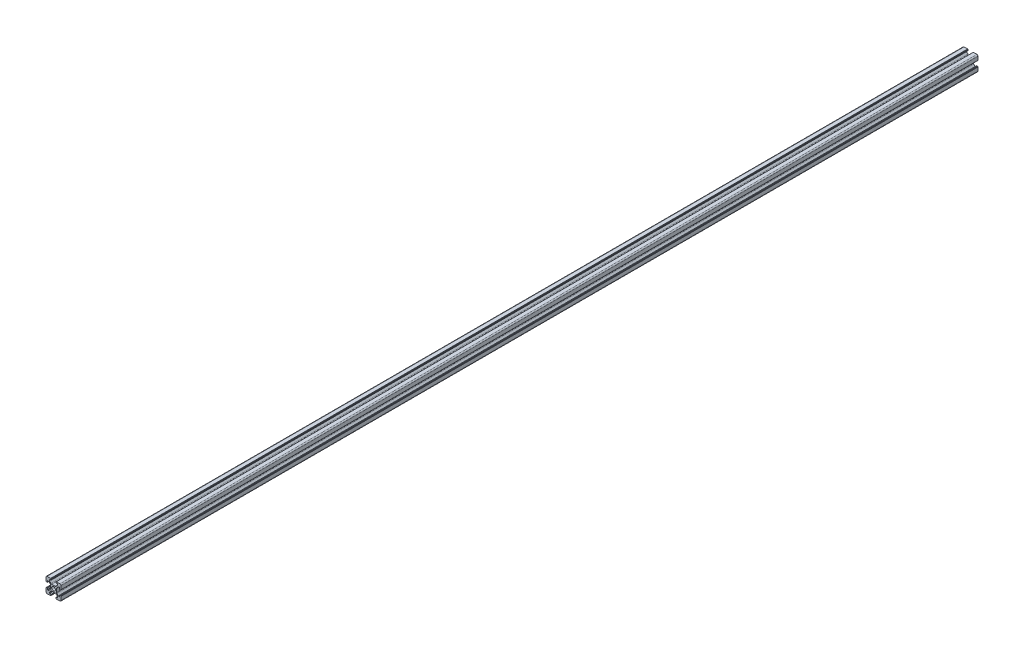
SolidWorks part; units mm, degrees
material "1060 Alloy"
ref_plane "前视基准面" through (0, 0, 0) normal (0, 0, 1) x (1, 0, 0)
ref_plane "上视基准面" through (0, 0, 0) normal (0, 1, 0) x (1, 0, 0)
ref_plane "右视基准面" through (0, 0, 0) normal (1, 0, 0) x (0, 0, -1)
sketch "草图1" plane through (0, 0, 0) normal (0, 0, 1) x (1, 0, 0)
  line L0 (0, 0) -> (0, 5.5) construction
  line L1 (-8.5023, -10.0023) -> (-3.85, -10.0023)
  line L2 (-10.0023, -8.5023) -> (-10.0023, -3.85)
  line L3 (-8.5023, 10.0023) -> (-3.85, 10.0023)
  line L4 (10.0023, -8.5023) -> (10.0023, -3.85)
  line L5 (-10.0023, -10.0023) -> (10.0023, 10.0023) construction
  line L6 (-10.0023, 10.0023) -> (10.0023, -10.0023) construction
  line L7 (-2.218, -3.9) -> (2.218, -3.9)
  line L8 (-3.9, -2.218) -> (-3.9, 2.218)
  line L9 (-2.218, 3.9) -> (2.218, 3.9)
  line L10 (3.9, -2.218) -> (3.9, 2.218)
  line L11 (-3.9, -3.9) -> (3.9, 3.9) construction
  line L12 (-3.9, 3.9) -> (3.9, -3.9) construction
  line L13 (-5.25, -8.2) -> (-3.35, -8.2)
  line L14 (-8.2, -5.25) -> (-8.2, -3.35)
  line L15 (-5.25, 8.2) -> (-3.35, 8.2)
  line L16 (8.2, -5.25) -> (8.2, -3.35)
  line L17 (-8.2, -8.2) -> (8.2, 8.2) construction
  line L18 (-8.2, 8.2) -> (8.2, -8.2) construction
  line L19 (-7.95, 5.5) -> (-6.6642, 5.5)
  line L20 (0, 0) -> (5.5, 0) construction
  line L23 (-5.5, 7.95) -> (-5.5, 6.6642)
  line L26 (0, 0) -> (-0.5303, 0.5303)
  line L27 (3.2787, 4.3393) -> (5.4268, 6.4874)
  line L28 (0, 0) -> (0.5303, -0.5303)
  line L29 (5.5, 6.6642) -> (5.5, 7.95)
  line L30 (4.3393, 3.2787) -> (6.4874, 5.4268)
  line L31 (6.6642, 5.5) -> (7.95, 5.5)
  line L32 (4.3393, -3.2787) -> (6.4874, -5.4268)
  line L33 (3.2787, -4.3393) -> (5.4268, -6.4874)
  line L34 (-3.2787, -4.3393) -> (-5.4268, -6.4874)
  line L35 (-4.3393, -3.2787) -> (-6.4874, -5.4268)
  line L36 (-4.3393, 3.2787) -> (-6.4874, 5.4268)
  line L37 (-3.2787, 4.3393) -> (-5.4268, 6.4874)
  line L38 (3.1, -8.45) -> (3.1, -9.2523)
  line L39 (8.45, 3.1) -> (9.2523, 3.1)
  line L40 (-5.5, -6.6642) -> (-5.5, -7.95)
  line L41 (-6.6642, -5.5) -> (-7.95, -5.5)
  line L42 (5.5, -6.6642) -> (5.5, -7.95)
  line L43 (6.6642, -5.5) -> (7.95, -5.5)
  line L44 (9.2523, -3.1) -> (8.45, -3.1)
  line L46 (10.0023, 3.85) -> (10.0023, 8.5023)
  line L47 (8.2, 3.35) -> (8.2, 5.25)
  line L48 (-3.1, -9.2523) -> (-3.1, -8.45)
  line L49 (-8.45, -3.1) -> (-9.2523, -3.1)
  line L50 (-9.2523, 3.1) -> (-8.45, 3.1)
  line L51 (-3.1, 8.45) -> (-3.1, 9.2523)
  line L52 (3.1, 9.2523) -> (3.1, 8.45)
  line L53 (3.85, 10.0023) -> (8.5023, 10.0023)
  line L54 (3.35, 8.2) -> (5.25, 8.2)
  line L55 (-10.0023, 3.85) -> (-10.0023, 8.5023)
  line L56 (-8.2, 3.35) -> (-8.2, 5.25)
  line L57 (3.35, -8.2) -> (5.25, -8.2)
  line L58 (3.85, -10.0023) -> (8.5023, -10.0023)
  line L59 (9.7523, -3.6) -> (9.5023, -3.6)
  line L61 (9.7523, 3.6) -> (9.5023, 3.6)
  line L62 (9.5023, -3.6) -> (9.5023, -3.35)
  line L63 (3.6, -9.7523) -> (3.6, -9.5023)
  line L64 (3.35, -9.5023) -> (3.6, -9.5023)
  line L65 (9.5023, 3.35) -> (9.5023, 3.6)
  line L66 (-3.6, -9.5023) -> (-3.35, -9.5023)
  line L67 (-3.6, -9.7523) -> (-3.6, -9.5023)
  line L68 (-9.7523, -3.6) -> (-9.5023, -3.6)
  line L69 (-9.5023, -3.35) -> (-9.5023, -3.6)
  line L70 (-9.5023, 3.6) -> (-9.5023, 3.35)
  line L71 (-9.7523, 3.6) -> (-9.5023, 3.6)
  line L72 (-3.6, 9.7523) -> (-3.6, 9.5023)
  line L73 (-3.35, 9.5023) -> (-3.6, 9.5023)
  line L74 (3.6, 9.5023) -> (3.35, 9.5023)
  line L75 (3.6, 9.7523) -> (3.6, 9.5023)
  circle A0 centre (0, 0) radius 2.5
  arc A1 (10.0023, 8.5023) -> (8.5023, 10.0023) centre (8.5023, 8.5023) ccw
  arc A2 (8.5023, -10.0023) -> (10.0023, -8.5023) centre (8.5023, -8.5023) ccw
  arc A3 (-10.0023, -8.5023) -> (-8.5023, -10.0023) centre (-8.5023, -8.5023) ccw
  arc A4 (-10.0023, 8.5023) -> (-8.5023, 10.0023) centre (-8.5023, 8.5023) cw
  arc A5 (-9.5023, -3.35) -> (-9.2523, -3.1) centre (-9.2523, -3.35) cw
  arc A6 (-9.7523, -3.6) -> (-10.0023, -3.85) centre (-9.7523, -3.85) ccw
  arc A7 (-8.45, -3.1) -> (-8.2, -3.35) centre (-8.45, -3.35) cw
  arc A8 (-7.95, -5.5) -> (-8.2, -5.25) centre (-7.95, -5.25) cw
  arc A9 (-6.4874, -5.4268) -> (-6.6642, -5.5) centre (-6.6642, -5.25) cw
  arc A10 (-5.4268, -6.4874) -> (-5.5, -6.6642) centre (-5.25, -6.6642) ccw
  arc A11 (-5.5, -7.95) -> (-5.25, -8.2) centre (-5.25, -7.95) ccw
  arc A12 (-3.6, -9.7523) -> (-3.85, -10.0023) centre (-3.85, -9.7523) cw
  arc A13 (-3.35, -9.5023) -> (-3.1, -9.2523) centre (-3.35, -9.2523) ccw
  arc A14 (-3.1, -8.45) -> (-3.35, -8.2) centre (-3.35, -8.45) ccw
  arc A15 (3.1, -8.45) -> (3.35, -8.2) centre (3.35, -8.45) cw
  arc A16 (5.5, -7.95) -> (5.25, -8.2) centre (5.25, -7.95) cw
  arc A17 (5.4268, -6.4874) -> (5.5, -6.6642) centre (5.25, -6.6642) cw
  arc A18 (6.4874, -5.4268) -> (6.6642, -5.5) centre (6.6642, -5.25) ccw
  arc A19 (7.95, -5.5) -> (8.2, -5.25) centre (7.95, -5.25) ccw
  arc A20 (8.45, -3.1) -> (8.2, -3.35) centre (8.45, -3.35) ccw
  arc A21 (9.5023, -3.35) -> (9.2523, -3.1) centre (9.2523, -3.35) ccw
  arc A22 (9.7523, -3.6) -> (10.0023, -3.85) centre (9.7523, -3.85) cw
  arc A23 (3.35, -9.5023) -> (3.1, -9.2523) centre (3.35, -9.2523) cw
  arc A24 (3.6, -9.7523) -> (3.85, -10.0023) centre (3.85, -9.7523) ccw
  arc A25 (7.95, 5.5) -> (8.2, 5.25) centre (7.95, 5.25) cw
  arc A26 (8.2, 3.35) -> (8.45, 3.1) centre (8.45, 3.35) ccw
  arc A27 (9.5023, 3.35) -> (9.2523, 3.1) centre (9.2523, 3.35) cw
  arc A28 (9.7523, 3.6) -> (10.0023, 3.85) centre (9.7523, 3.85) ccw
  arc A29 (6.6642, 5.5) -> (6.4874, 5.4268) centre (6.6642, 5.25) ccw
  arc A30 (5.4268, 6.4874) -> (5.5, 6.6642) centre (5.25, 6.6642) ccw
  arc A31 (5.5, 7.95) -> (5.25, 8.2) centre (5.25, 7.95) ccw
  arc A32 (3.1, 8.45) -> (3.35, 8.2) centre (3.35, 8.45) ccw
  arc A33 (3.6, 9.7523) -> (3.85, 10.0023) centre (3.85, 9.7523) cw
  arc A34 (3.35, 9.5023) -> (3.1, 9.2523) centre (3.35, 9.2523) ccw
  arc A35 (-9.7523, 3.6) -> (-10.0023, 3.85) centre (-9.7523, 3.85) cw
  arc A36 (-9.5023, 3.35) -> (-9.2523, 3.1) centre (-9.2523, 3.35) ccw
  arc A37 (-8.45, 3.1) -> (-8.2, 3.35) centre (-8.45, 3.35) ccw
  arc A38 (-8.2, 5.25) -> (-7.95, 5.5) centre (-7.95, 5.25) cw
  arc A39 (-6.4874, 5.4268) -> (-6.6642, 5.5) centre (-6.6642, 5.25) ccw
  arc A40 (-5.4268, 6.4874) -> (-5.5, 6.6642) centre (-5.25, 6.6642) cw
  arc A41 (-5.5, 7.95) -> (-5.25, 8.2) centre (-5.25, 7.95) cw
  arc A42 (-3.1, 8.45) -> (-3.35, 8.2) centre (-3.35, 8.45) cw
  arc A43 (-3.1, 9.2523) -> (-3.35, 9.5023) centre (-3.35, 9.2523) ccw
  arc A44 (-3.6, 9.7523) -> (-3.85, 10.0023) centre (-3.85, 9.7523) ccw
  arc A45 (-4.3393, 3.2787) -> (-3.9, 2.218) centre (-5.4, 2.218) cw
  arc A46 (-3.2787, 4.3393) -> (-2.218, 3.9) centre (-2.218, 5.4) ccw
  arc A47 (3.2787, 4.3393) -> (2.218, 3.9) centre (2.218, 5.4) cw
  arc A48 (4.3393, 3.2787) -> (3.9, 2.218) centre (5.4, 2.218) ccw
  arc A49 (4.3393, -3.2787) -> (3.9, -2.218) centre (5.4, -2.218) cw
  arc A50 (3.2787, -4.3393) -> (2.218, -3.9) centre (2.218, -5.4) ccw
  arc A51 (-4.3393, -3.2787) -> (-3.9, -2.218) centre (-5.4, -2.218) ccw
  arc A52 (-2.218, -3.9) -> (-3.2787, -4.3393) centre (-2.218, -5.4) ccw
  point P0 (0, 0)
  point P7 (10.0023, 0)
  point P62 (0, 0)
  point P76 (0, 0)
  point P92 (-8.2, -5.5)
  point P99 (0, 0)
  point P106 (-5.5, -8.2)
  point P117 (5.5, -8.2)
  point P124 (8.2, -5.5)
  point P137 (8.2, 5.5)
  point P140 (8.2, 3.1)
  point P147 (6.5607, 5.5)
  point P152 (5.5, 8.2)
  point P167 (-8.2, 5.5)
  point P174 (-5.5, 8.2)
  dimension "D1" = 1.5
  dimension "D5" = 0.25
  dimension "D6" = 1.5
  dimension "D2" = 4
  dimension "D3" = 4
  dimension "D4" = 4
extrude "凸台-拉伸1" add sketch "草图1" along normal blind 1220 contours A52 L7 A50 L33 A17 L42 A16 L57 A15 L38 A23 L64 L63 A24 L58 A2 L4 A22 L59 L62 A21 L44 A20 L16 A19 L43 A18 L32 A49 L10 A48 L30 A29 L31 A25 L47 A26 L39 A27 L65 L61 A28 L46 A1 L53 A33 L75 L74 A34 L52 A32
ref_plane "Plane1" through (0, 0, 610) normal (0, 0, 1) x (1, 0, 0)
